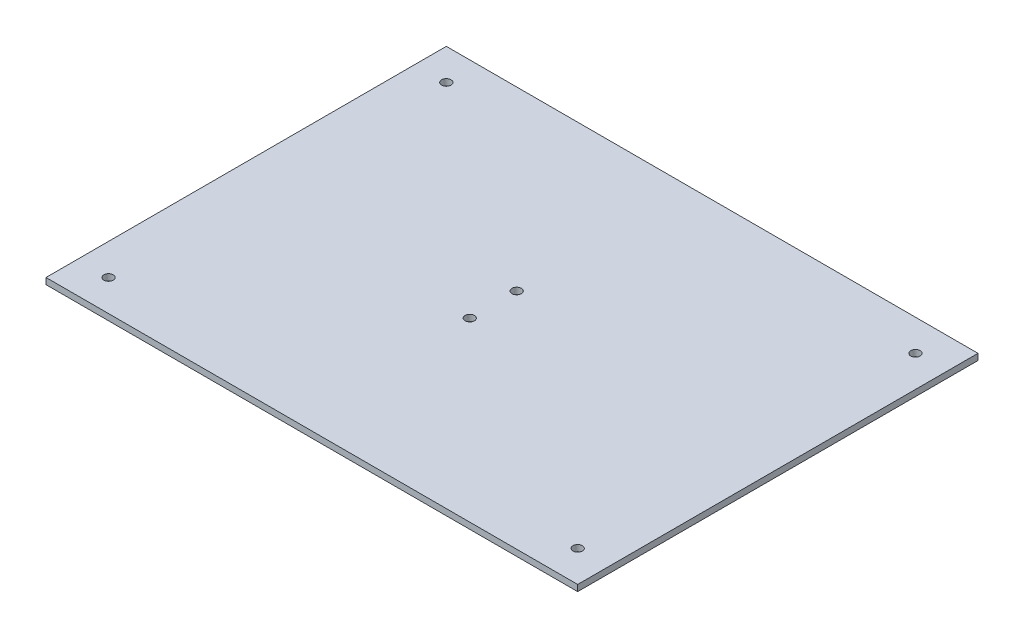
SolidWorks part; units mm, degrees
ref_plane "Спереди" through (0, 0, 0) normal (0, 0, 1) x (1, 0, 0)
ref_plane "Сверху" through (0, 0, 0) normal (0, 1, 0) x (1, 0, 0)
ref_plane "Справа" through (0, 0, 0) normal (1, 0, 0) x (0, 0, -1)
sketch "Эскиз1" plane through (0, 0, 0) normal (0, 1, 0) x (1, 0, 0)
  line L0 (10.6415, 53.6415) -> (10.6415, -74.3585) construction
  line L1 (-74.3585, 53.6415) -> (95.6415, 53.6415)
  line L2 (-74.3585, 53.6415) -> (-74.3585, -74.3585)
  line L3 (-74.3585, -74.3585) -> (95.6415, -74.3585)
  line L4 (95.6415, 53.6415) -> (95.6415, -74.3585)
  line L5 (-74.3585, -10.3585) -> (95.6415, -10.3585) construction
  circle A0 centre (-64.3585, 43.6415) radius 1.5
  circle A1 centre (85.6415, 43.6415) radius 1.5
  circle A2 centre (85.6415, -64.3585) radius 1.5
  circle A3 centre (-64.3585, -64.3585) radius 1.5
  point P0 (0, 0)
  point P12 (10.6415, -10.3585)
  dimension "D1" = 10
  dimension "D2" = 10
  dimension "D3" = 128
  dimension "D4" = 170
extrude "Бобышка-Вытянуть1" add sketch "Эскиз1" along normal blind 2
sketch "Эскиз2" plane through (0, 2, 0) normal (0, 1, 0) x (1, 0, 0)
  line L0 (10.6415, 53.6415) -> (10.6415, -74.3585) construction
  line L1 (95.6415, 53.6415) -> (-74.3585, 53.6415) construction
  line L2 (-74.3585, -74.3585) -> (95.6415, -74.3585) construction
  line L3 (-74.3585, -10.3585) -> (95.6415, -10.3585) construction
  line L4 (-74.3585, 53.6415) -> (-74.3585, -74.3585) construction
  line L5 (95.6415, -74.3585) -> (95.6415, 53.6415) construction
  circle A0 centre (4.6415, -17.8585) radius 1.5
  circle A1 centre (4.6415, -2.8585) radius 1.5
  dimension "D1" = 3
  dimension "D2" = 6
  dimension "D3" = 7.5
extrude "Вырез-Вытянуть1" cut sketch "Эскиз2" against normal through all
